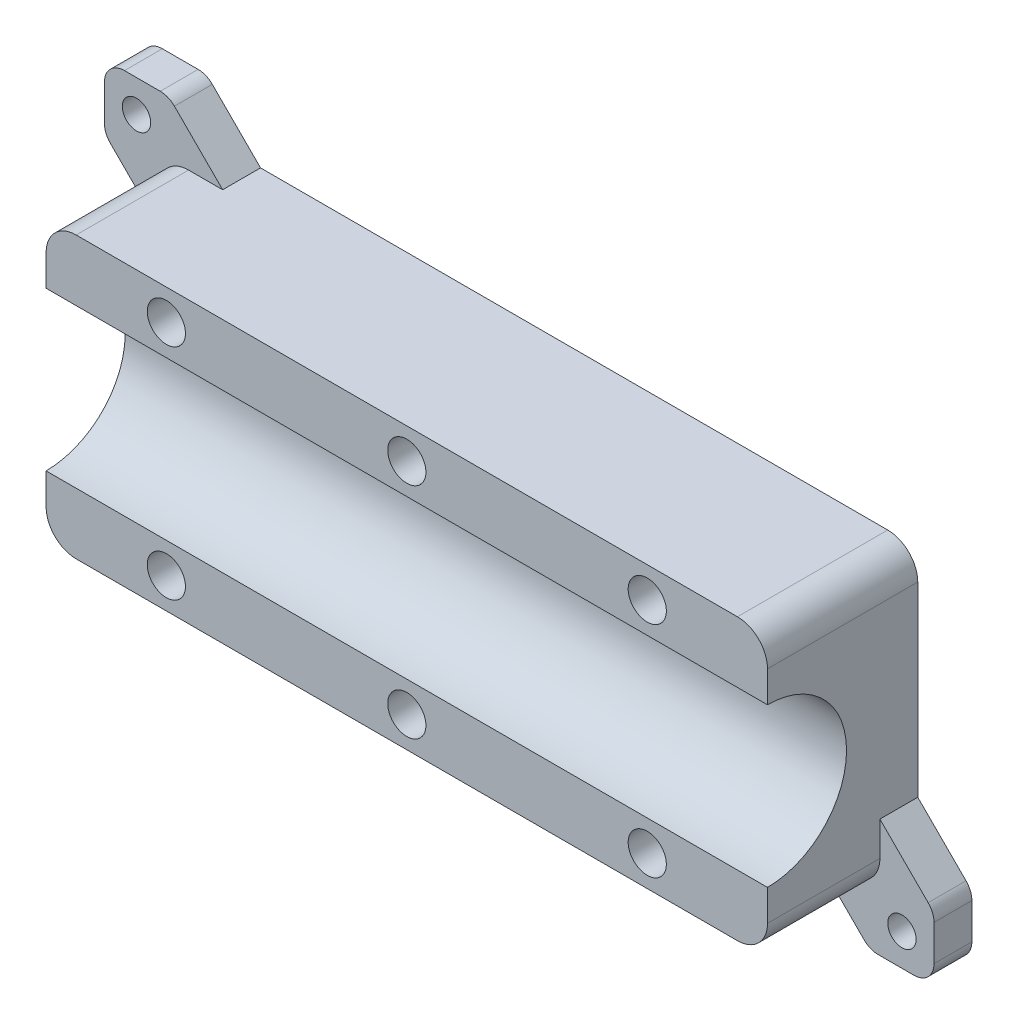
SolidWorks part; units mm, degrees
material "ABS"
ref_plane "X-Y Datum" through (0, 0, 0) normal (0, 0, 1) x (1, 0, 0)
ref_plane "X-Z Datum" through (0, 0, 0) normal (0, 1, 0) x (1, 0, 0)
ref_plane "Y-Z Datum" through (0, 0, 0) normal (1, 0, 0) x (0, 0, -1)
sketch "Sketch1" plane through (0, 0, 0) normal (0, 0, 1) x (1, 0, 0)
  line L1 (-57.15, 22.225) -> (57.15, 22.225)
  line L2 (-57.15, 22.225) -> (-57.15, -22.225)
  line L3 (-57.15, -22.225) -> (57.15, -22.225)
  line L4 (57.15, 22.225) -> (57.15, -22.225)
  line L5 (-57.15, 22.225) -> (57.15, -22.225) construction
  line L6 (-57.15, -22.225) -> (57.15, 22.225) construction
  point P0 (0, 0)
  dimension "D1" = 114.3
  dimension "D2" = 44.45
extrude "Boss-Extrude1" add sketch "Sketch1" along normal blind 5
sketch "Sketch2" plane through (-57.15, 0, 0) normal (-1, 0, 0) x (0, 0, 1)
  line L0 (5, -22.225) -> (0, -22.225) construction
  line L1 (5, 22.225) -> (23.8125, 22.225)
  line L2 (5, 22.225) -> (5, -22.225)
  line L3 (5, -22.225) -> (23.8125, -22.225)
  line L4 (23.8125, 22.225) -> (23.8125, -22.225)
  circle A0 centre (23.8125, 0) radius 12.0269 construction
  circle A1 centre (23.8125, 0) radius 12.0269 construction
  circle A2 centre (23.8125, 0) radius 12.5269
  line M9 (5, -22.225) -> (5, 22.225)
  dimension "D1" = 0.5
extrude "Boss-Extrude2" add sketch "Sketch2" against normal blind 114.3 contours A2 L4 L1 L3 M9
sketch "Sketch3" plane through (0, 0, 23.8125) normal (0, 0, 1) x (1, 0, 0)
  line L0 (-57.15, 17.376) -> (57.15, 17.376) construction
  line L1 (-57.15, 22.225) -> (-57.15, 12.5269) construction
  line L2 (57.15, 22.225) -> (57.15, 12.5269) construction
  circle A0 centre (0, 17.376) radius 3.025
  dimension "D1" = 6.05
extrude "Cut-Extrude1" cut sketch "Sketch3" against normal blind 8
pattern_linear "LPattern1" count 2 spacing 38.1 along (1, 0, 0) count 2 spacing 38.1 along (-1, 0, 0) of "Cut-Extrude1"
mirror "Mirror1" about plane through (0, 0, 0) normal (0, 1, 0) of "LPattern1", "Cut-Extrude1"
sketch "Sketch4" plane through (0, 0, 0) normal (0, 0, 1) x (1, 0, 0)
  line L0 (55.5625, -20.6375) -> (65.7225, -30.7975) construction
  line L5 (-65.7225, 20.6375) -> (-55.5625, 20.6375)
  line L6 (-65.7225, 20.6375) -> (-65.7225, 30.7975)
  line L7 (-65.7225, 30.7975) -> (-55.5625, 30.7975)
  line L8 (-55.5625, 20.6375) -> (-55.5625, 30.7975)
  line L9 (55.5625, -30.7975) -> (65.7225, -30.7975)
  line L10 (55.5625, -30.7975) -> (55.5625, -20.6375)
  line L11 (55.5625, -20.6375) -> (65.7225, -20.6375)
  line L12 (65.7225, -30.7975) -> (65.7225, -20.6375)
  line L13 (-65.7225, 30.7975) -> (-55.5625, 20.6375)
  line L14 (57.15, 22.225) -> (-57.15, 22.225) construction
  line L15 (-57.15, 22.225) -> (-57.15, 12.5269) construction
  line L16 (57.15, -12.5269) -> (57.15, -22.225) construction
  line L17 (57.15, -22.225) -> (-57.15, -22.225) construction
  line L18 (-55.5625, 30.7975) -> (-46.99, 22.225)
  line L19 (-65.7225, 20.6375) -> (-55.5625, 30.7975)
  line L20 (-65.7225, 20.6375) -> (-57.15, 12.065)
  line L21 (55.5625, -30.7975) -> (46.99, -22.225)
  line L22 (65.7225, -20.6375) -> (55.5625, -30.7975) construction
  line L23 (65.7225, -20.6375) -> (57.15, -12.065)
  line L24 (57.15, -10.7701) -> (57.15, -22.225)
  line L25 (57.15, -22.225) -> (-57.15, -22.225)
  line L26 (-57.15, 22.225) -> (-57.15, 10.3851)
  line L27 (57.15, 22.225) -> (-57.15, 22.225)
  line L28 (-57.15, 12.5269) -> (-57.15, -12.5269) construction
  line L29 (57.15, -12.5269) -> (57.15, 12.5269) construction
  circle A0 centre (60.6425, -25.7175) radius 2 construction
  circle A1 centre (-60.6425, 25.7175) radius 2 construction
  dimension "D1" = 4
  dimension "D2" = 4
  dimension "D3" = 10.16
  dimension "D4" = 10.16
  dimension "D5" = 10.16
  dimension "D6" = 10.16
  dimension "D7" = 1.5875
  dimension "D8" = 1.5875
  dimension "D9" = 1.5875
  dimension "D10" = 1.5875
extrude "Boss-Extrude3" add sketch "Sketch4" along normal blind 6 contours L13 L6 L5 | L7 L13 L8 | L9 L12 L11 L10 | L27 L8 L19 L13 | L27 L18 L8 | L26 L13 L19 L5 | L26 L5 L20 | L23 L24 L11 | L10 L25 L21
hole_wizard "M4 Clearance Hole1" positions "Sketch5" profile "Sketch6" hole size "M4" standard "ANSI Metric" end condition through all
sketch "Sketch5" plane through (0, 0, 6) normal (0, 0, 1) x (1, 0, 0)
  point P2 (-60.6425, 25.7175)
  point P5 (60.6425, -25.7175)
sketch "Sketch6" plane through (-60.6425, 25.7175, 6) normal (1, 0, 0) x (0, -1, 0)
  line L0 (0, 0) -> (0, 6)
  line L1 (0, 6) -> (2.25, 6)
  line L2 (2.25, 6) -> (2.25, 0)
  line L5 (2.25, 0) -> (0, 0)
  line L11 (0, -6.35) -> (0, 107.95) construction
  dimension "Thru Hole Dia." = 4.5
  dimension "Thru Hole Depth" = 6
fillet "Fillet3" radius 3.175 6 edges at (-55.5625, 30.7975, 3) (-65.7225, 30.7975, 3) (-65.7225, 20.6375, 3) (65.7225, -20.6375, 3) (65.7225, -30.7975, 3) (55.5625, -30.7975, 3)
fillet "Fillet4" radius 4.7625 4 edges at (57.15, 22.225, 11.9062) (-57.15, 22.225, 14.9062) (57.15, -22.225, 14.9062) (-57.15, -22.225, 11.9062)
